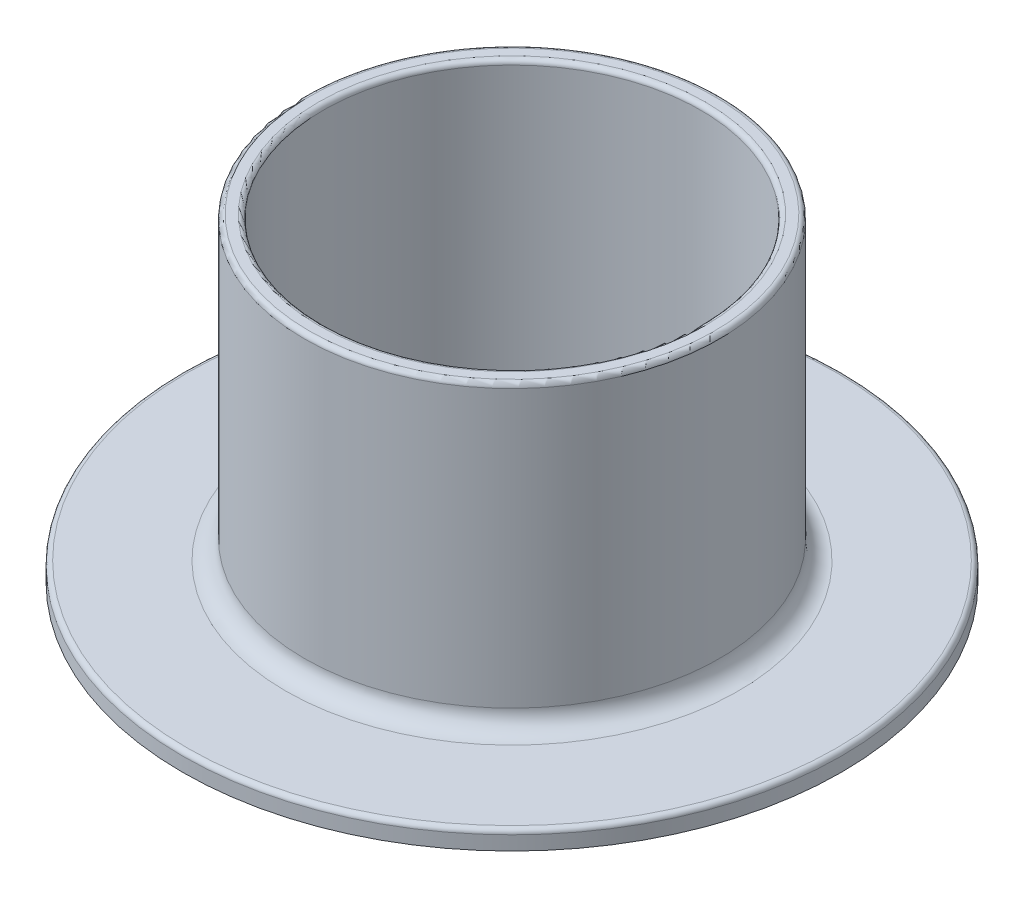
SolidWorks part; units mm, degrees
ref_plane "Front Plane" through (0, 0, 0) normal (0, 0, 1) x (1, 0, 0)
ref_plane "Top Plane" through (0, 0, 0) normal (0, 1, 0) x (1, 0, 0)
ref_plane "Right Plane" through (0, 0, 0) normal (1, 0, 0) x (0, 0, -1)
sketch "Sketch1" plane through (0, 0, 0) normal (0, 0, 1) x (1, 0, 0)
  line L0 (22.125, 33.5) -> (22.125, 4)
  line L1 (24.125, 2) -> (34.625, 2)
  line L2 (35.125, 1.5) -> (35.125, 0)
  line L3 (35.125, 0) -> (20.125, 0)
  line L4 (20.125, 0) -> (20.125, 33.5)
  line L5 (20.625, 34) -> (21.625, 34)
  line L6 (0, 40.7647) -> (0, 0) construction
  line L7 (0, 0) -> (20.125, 0) construction
  arc A0 (22.125, 4) -> (24.125, 2) centre (24.125, 4) ccw
  arc A2 (34.625, 2) -> (35.125, 1.5) centre (34.625, 1.5) cw
  arc A3 (22.125, 33.5) -> (21.625, 34) centre (21.625, 33.5) ccw
  arc A4 (20.125, 33.5) -> (20.625, 34) centre (20.625, 33.5) cw
  point P11 (22.125, 2)
  point P17 (35.125, 2)
  point P20 (22.125, 34)
  point P23 (20.125, 34)
  dimension "D6" = 2
  dimension "D8" = 0.5
  dimension "D1" = 40.25
  dimension "D2" = 34
  dimension "D3" = 2
  dimension "D4" = 2
  dimension "D5" = 13
revolve "Revolve1" add sketch "Sketch1" angle 360 about L6
